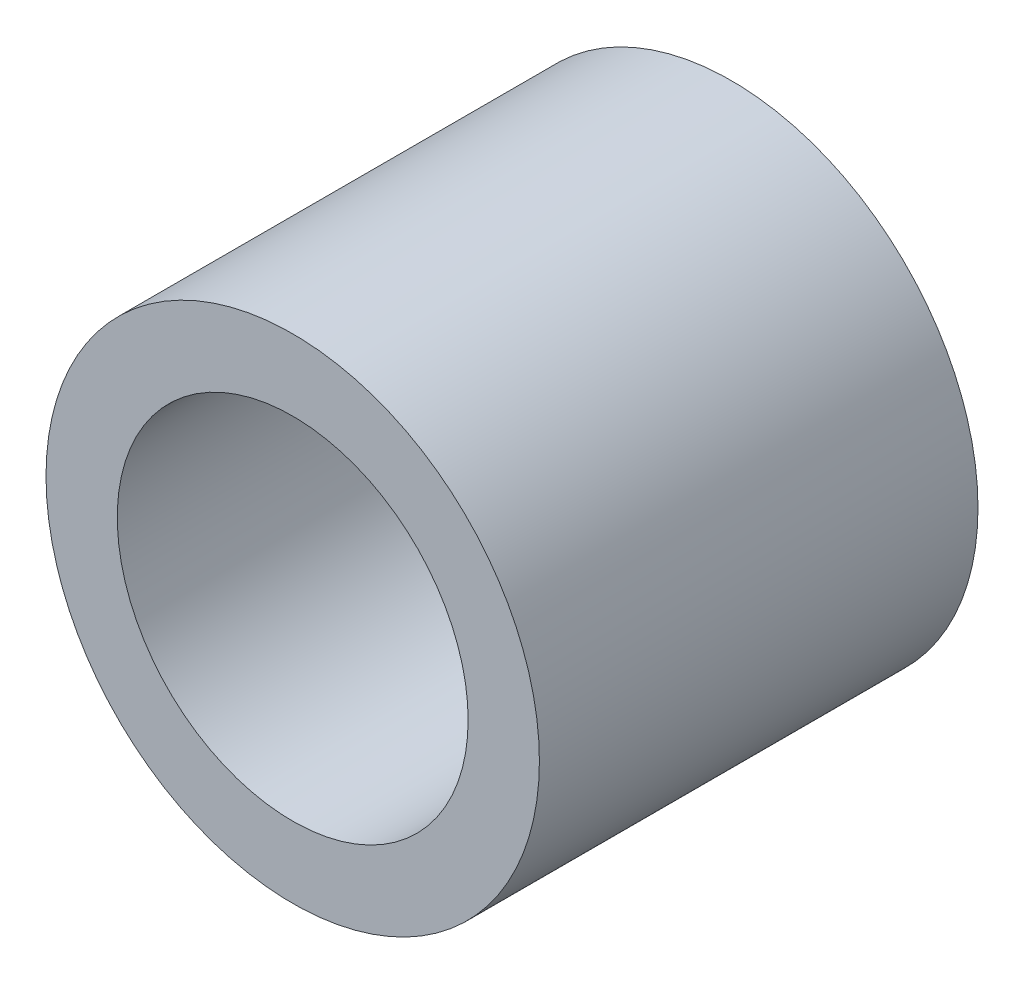
SolidWorks part; units mm, degrees
ref_plane "Front Plane" through (0, 0, 0) normal (0, 0, 1) x (1, 0, 0)
ref_plane "Top Plane" through (0, 0, 0) normal (0, 1, 0) x (1, 0, 0)
ref_plane "Right Plane" through (0, 0, 0) normal (1, 0, 0) x (0, 0, -1)
sketch "Sketch1" plane through (0, 0, 0) normal (0, 0, 1) x (1, 0, 0)
  circle A0 centre (0, 0) radius 2.25
  circle A1 centre (0, 0) radius 1.6
  dimension "OD" = 4.5
  dimension "ID" = 3.2
extrude "Extrude1" add sketch "Sketch1" along normal mid plane 4
sketch "Sketch2" plane through (0, 0, 0) normal (1, 0, 0) x (0, 0, -1)
  line L0 (-2, -1.6) -> (2, -1.6) construction
  line L3 (2, 1.6) -> (-2, 1.6) construction
  line L5 (-2, -1.6) -> (2, -1.6)
  line L6 (2, 1.6) -> (-2, 1.6)
sketch "Sketch4" plane through (0, 0, 2) normal (0, 0, 1) x (1, 0, 0)
  line L0 (0, 0) -> (-1.1314, 1.1314)
  line L1 (0, -1.1) -> (0, 1.1) construction
  circle A0 centre (0, 0) radius 1.6 construction
  dimension "D1" = 45
